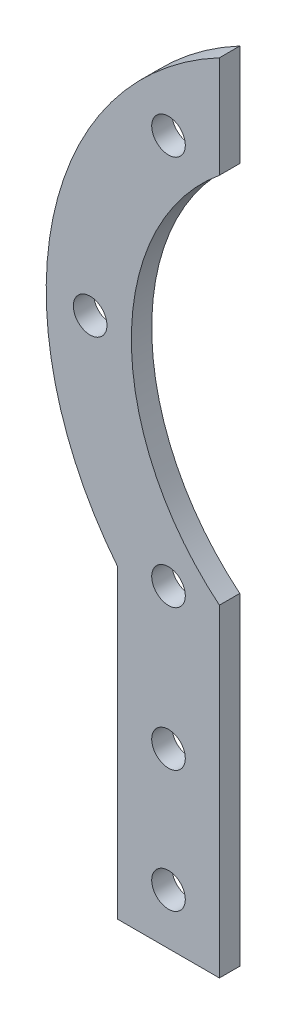
SolidWorks part; units mm, degrees
ref_plane "前视基准面" through (0, 0, 0) normal (0, 0, 1) x (1, 0, 0)
ref_plane "上视基准面" through (0, 0, 0) normal (0, 1, 0) x (1, 0, 0)
ref_plane "右视基准面" through (0, 0, 0) normal (1, 0, 0) x (0, 0, -1)
sketch "草图1" plane through (0, 0, 0) normal (0, 0, 1) x (1, 0, 0)
  line L0 (10, 68.2843) -> (10, 78.2843)
  line L1 (0, 0) -> (10, 0)
  line L2 (0, 0) -> (0, 30)
  line L4 (10, 0) -> (10, 31.7157)
  arc A0 (10, 68.2843) -> (10, 31.7157) centre (25, 50) ccw
  arc A1 (10, 78.2843) -> (0, 30) centre (25, 50) ccw
  circle A2 centre (5, 5) radius 1.65
  circle A3 centre (5, 17) radius 1.65
  arc A4 (10, 73.2843) -> (10, 26.7157) centre (25, 50) ccw construction
  circle A5 centre (-2.6976, 50) radius 1.65
  circle A6 centre (5, 69.1613) radius 1.65
  circle A7 centre (5, 30.8387) radius 1.65
  point P12 (10, 73.2843)
  point P21 (0, 0)
  point P22 (0, 0)
  point P23 (0, 0)
  point P24 (0, 0)
  point P25 (5, 0)
  dimension "D6" = 3.3
  dimension "D7" = 3.3
  dimension "D10" = 3.3
  dimension "D11" = 3.3
  dimension "D12" = 3.3
  dimension "D1" = 10
  dimension "D2" = 30
  dimension "D3" = 15
  dimension "D4" = 50
  dimension "D5" = 12
  dimension "D8" = 5
  dimension "D9" = 10
  dimension "D13" = 5
extrude "凸台-拉伸1" add sketch "草图1" along normal blind 2
